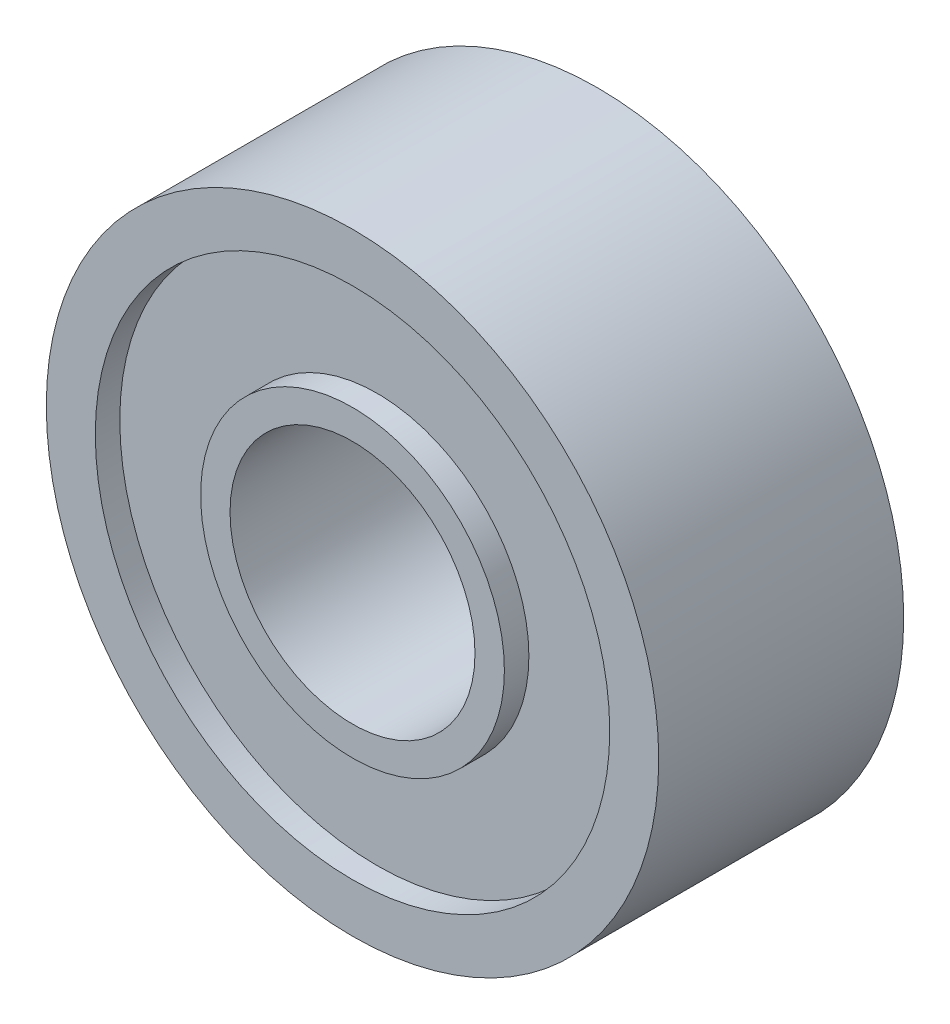
SolidWorks part; units mm, degrees
ref_plane "Front Plane" through (0, 0, 0) normal (0, 0, 1) x (1, 0, 0)
ref_plane "Top Plane" through (0, 0, 0) normal (0, 1, 0) x (1, 0, 0)
ref_plane "Right Plane" through (0, 0, 0) normal (1, 0, 0) x (0, 0, -1)
sketch "Sketch1" plane through (0, 0, 0) normal (0, 0, 1) x (1, 0, 0)
  circle A0 centre (0, 0) radius 5
  circle A1 centre (0, 0) radius 12.5
  dimension "D1" = 10
  dimension "D2" = 25
extrude "Boss-Extrude1" add sketch "Sketch1" along normal mid plane 10
sketch "Sketch2" plane through (0, 0, 5) normal (0, 0, 1) x (1, 0, 0)
  circle A4 centre (0, 0) radius 10.5
  circle A5 centre (0, 0) radius 6.2
  circle A6 centre (0, 0) radius 12.5 construction
  circle A7 centre (0, 0) radius 5 construction
  dimension "D1" = 2
  dimension "D2" = 1.2
extrude "Cut-Extrude1" cut sketch "Sketch2" against normal blind 1
mirror "Mirror1" about plane through (0, 0, 0) normal (0, 0, 1) of "Cut-Extrude1"
